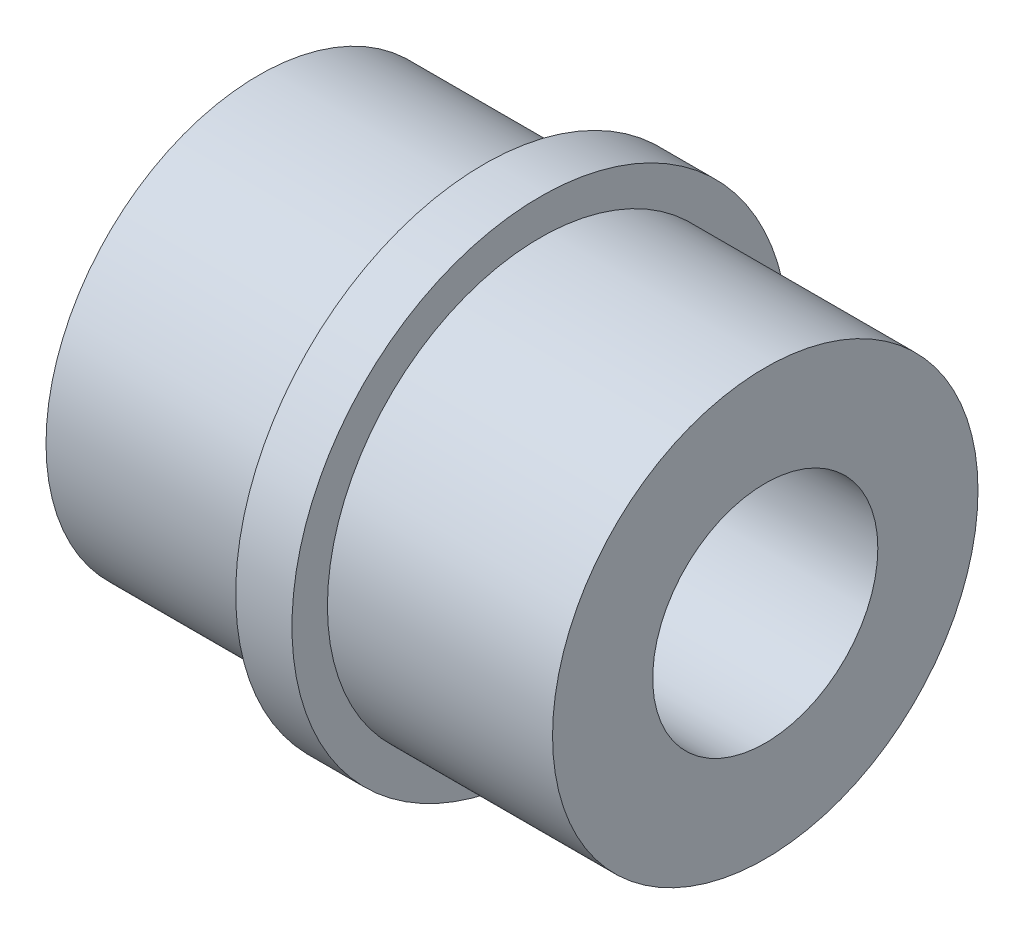
SolidWorks part; units mm, degrees
ref_plane "Front Plane" through (0, 0, 0) normal (0, 0, 1) x (1, 0, 0)
ref_plane "Top Plane" through (0, 0, 0) normal (0, 1, 0) x (1, 0, 0)
ref_plane "Right Plane" through (0, 0, 0) normal (1, 0, 0) x (0, 0, -1)
sketch "Sketch1" plane through (0, 0, 0) normal (1, 0, 0) x (0, 0, -1)
  circle A0 centre (0, 0) radius 6
  dimension "D1" = 12
extrude "Boss-Extrude1" add sketch "Sketch1" along normal blind 6.35
sketch "Sketch2" plane through (6.35, 0, 0) normal (1, 0, 0) x (0, 0, -1)
  circle A0 centre (0, 0) radius 7
  dimension "D1" = 14
extrude "Boss-Extrude2" add sketch "Sketch2" along normal blind 1.5875
sketch "Sketch3" plane through (7.9375, 0, 0) normal (1, 0, 0) x (0, 0, -1)
  circle A0 centre (0, 0) radius 6
  dimension "D1" = 12
extrude "Boss-Extrude3" add sketch "Sketch3" along normal blind 6.35
sketch "Sketch4" plane through (14.2875, 0, 0) normal (1, 0, 0) x (0, 0, -1)
  circle A0 centre (0, 0) radius 3.175
  dimension "D1" = 6.35
extrude "Cut-Extrude1" cut sketch "Sketch4" against normal through all
equation "\"wheelPitchD\"= 16mm"
equation "\"wheelClearanceD\"= 18mm"
equation "\"wormPitchD\"= 12mm"
equation "\"wormClearanceD\"= 14mm"
equation "\"D1@Sketch1\"=\"wormPitchD\""
equation "\"D1@Sketch2\"=\"wormClearanceD\""
equation "\"D1@Sketch3\"=\"wormPitchD\""
equation "\"ShaftD\"= 0.25in"
equation "\"D1@Sketch4\"=\"ShaftD\""
equation "\"MountingDistance\" = 14mm"
equation "\"HubDiameter\"= 12mm"
equation "\"HubWidth\"= 8mm"
equation "\"FaceWidth\"= 8mm"
